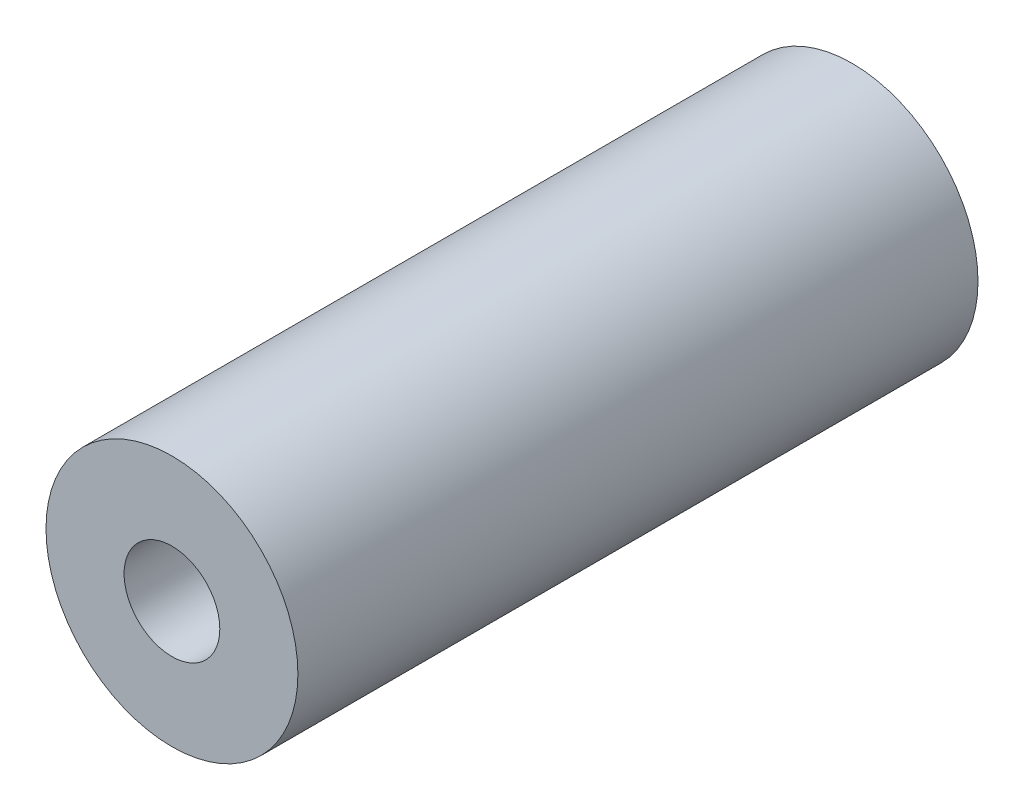
SolidWorks part; units mm, degrees
ref_plane "Front" through (0, 0, 0) normal (0, 0, 1) x (1, 0, 0)
ref_plane "Top" through (0, 0, 0) normal (0, 1, 0) x (1, 0, 0)
ref_plane "Right" through (0, 0, 0) normal (1, 0, 0) x (0, 0, -1)
sketch "Sketch2" plane through (0, 0, 0) normal (0, 0, 1) x (1, 0, 0)
  circle A0 centre (0, 0) radius 6.35
  circle A1 centre (0, 0) radius 2.413
  dimension "D1" = 4.826
  dimension "D2" = 12.7
extrude "Boss-Extrude1" add sketch "Sketch2" along normal blind 34.29
